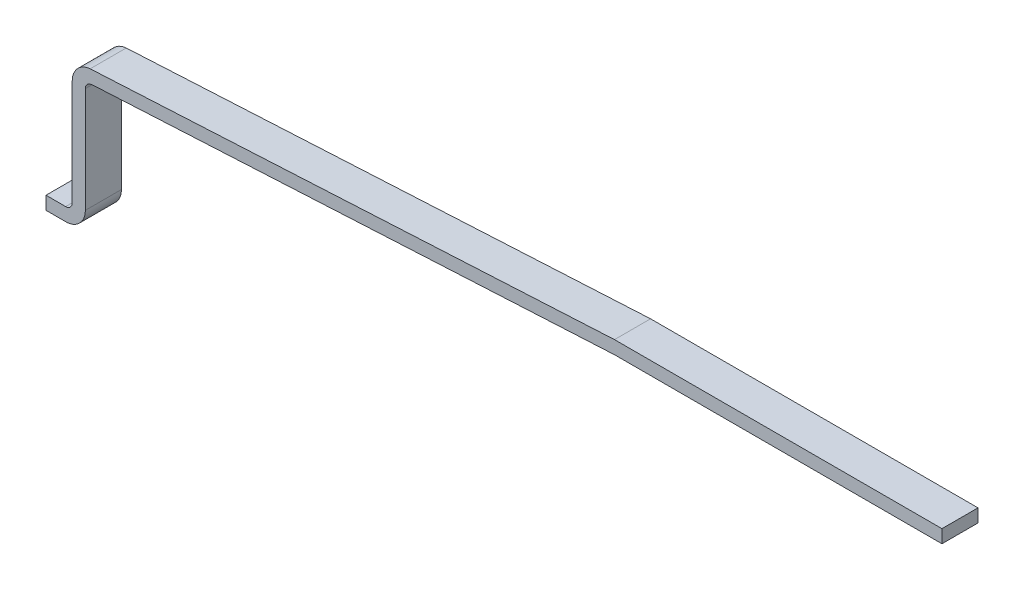
SolidWorks part; units mm, degrees
ref_plane "Plano frontal" through (0, 0, 0) normal (0, 0, 1) x (1, 0, 0)
ref_plane "Plano superior" through (0, 0, 0) normal (0, 1, 0) x (1, 0, 0)
ref_plane "Plano direito" through (0, 0, 0) normal (1, 0, 0) x (0, 0, -1)
sketch "Esboço1" plane through (0, 0, 0) normal (0, 0, 1) x (1, 0, 0)
  line L0 (-0.3192, 12.471) -> (-0.0192, 12.471)
  line L2 (0.0808, 12.571) -> (0.0808, 14.1794)
  line L4 (0.3547, 14.4783) -> (8.3544, 14.9)
  line L5 (8.3544, 14.9) -> (13.35, 14.9)
  line L6 (13.35, 14.9) -> (13.35, 14.7)
  line L7 (13.35, 14.7) -> (8.3544, 14.7)
  line L8 (8.3544, 14.7) -> (0.4324, 14.2851)
  line L9 (0.4324, 14.2851) -> (0.3721, 14.279)
  line L11 (0.2808, 14.1794) -> (0.2808, 12.571)
  line L14 (-0.0192, 12.271) -> (-0.3192, 12.271)
  line L15 (-0.3192, 12.271) -> (-0.3192, 12.471)
  arc A2 (-0.0192, 12.471) -> (0.0808, 12.571) centre (-0.0192, 12.571) ccw
  arc A3 (-0.0192, 12.271) -> (0.2808, 12.571) centre (-0.0192, 12.571) ccw
  arc A4 (0.3547, 14.4783) -> (0.0808, 14.1794) centre (0.3808, 14.1794) ccw
  arc A5 (0.2808, 14.1794) -> (0.3721, 14.279) centre (0.3808, 14.1794) cw
extrude "Ressalto-extrusão1" add sketch "Esboço1" along normal blind 0.55
